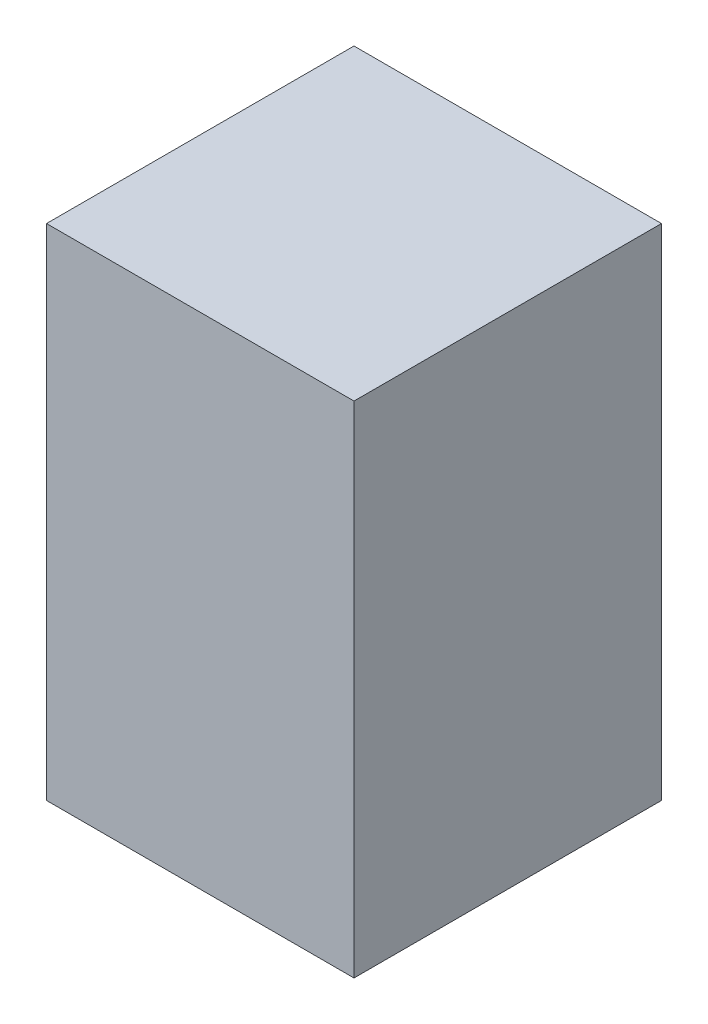
SolidWorks part; units mm, degrees
ref_plane "Front Plane" through (0, 0, 0) normal (0, 0, 1) x (1, 0, 0)
ref_plane "Top Plane" through (0, 0, 0) normal (0, 1, 0) x (1, 0, 0)
ref_plane "Right Plane" through (0, 0, 0) normal (1, 0, 0) x (0, 0, -1)
sketch "Sketch1" plane through (0, 0, 0) normal (0, 1, 0) x (1, 0, 0)
  line L1 (-36.4562, 352.0817) -> (369.9438, 352.0817)
  line L2 (-36.4562, 352.0817) -> (-36.4562, -54.3183)
  line L3 (-36.4562, -54.3183) -> (369.9438, -54.3183)
  line L4 (369.9438, 352.0817) -> (369.9438, -54.3183)
  dimension "D1" = 406.4
  dimension "D2" = 406.4
extrude "Boss-Extrude1" add sketch "Sketch1" along normal blind 660.4
